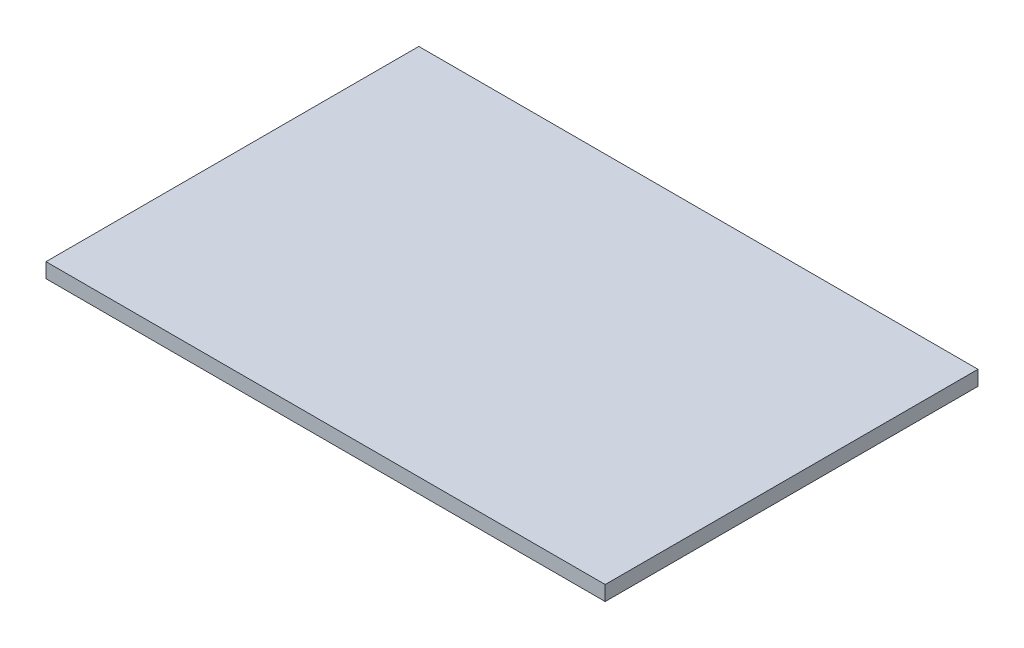
SolidWorks part; units mm, degrees
ref_plane "Front Plane" through (0, 0, 0) normal (0, 0, 1) x (1, 0, 0)
ref_plane "Top Plane" through (0, 0, 0) normal (0, 1, 0) x (1, 0, 0)
ref_plane "Right Plane" through (0, 0, 0) normal (1, 0, 0) x (0, 0, -1)
sketch "Sketch1" plane through (0, 0, 0) normal (0, 1, 0) x (1, 0, 0)
  line L1 (-30, -20) -> (30, -20)
  line L2 (-30, -20) -> (-30, 20)
  line L3 (-30, 20) -> (30, 20)
  line L4 (30, -20) -> (30, 20)
  line L5 (-30, -20) -> (30, 20) construction
  line L6 (-30, 20) -> (30, -20) construction
  point P0 (0, 0)
  dimension "D1" = 40
  dimension "D2" = 60
extrude "Boss-Extrude1" add sketch "Sketch1" along normal blind 1.5875
